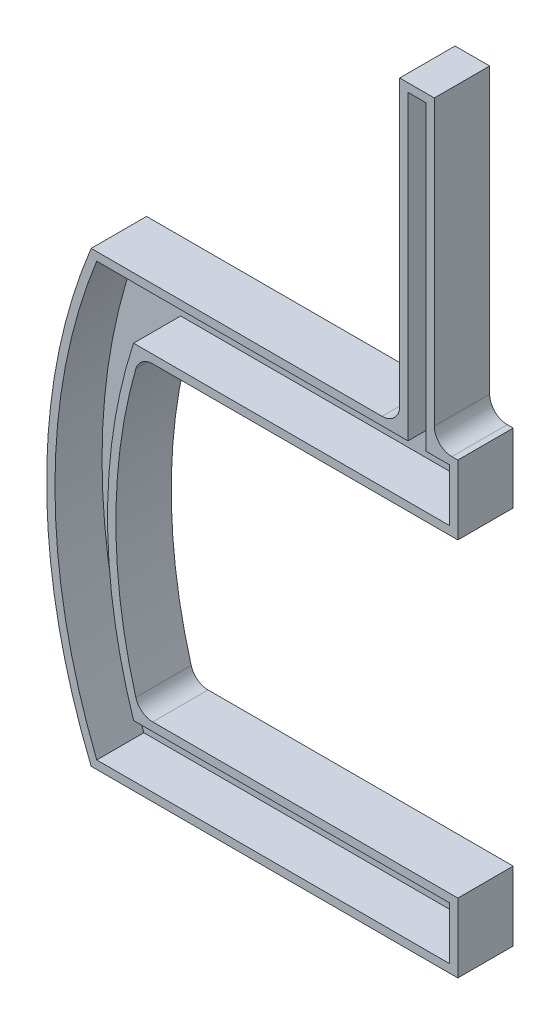
SolidWorks part; units mm, degrees
ref_plane "Front" through (0, 0, 0) normal (0, 0, 1) x (1, 0, 0)
ref_plane "Top" through (0, 0, 0) normal (0, 1, 0) x (1, 0, 0)
ref_plane "Right" through (0, 0, 0) normal (1, 0, 0) x (0, 0, -1)
sketch "Sketch1" plane through (0, 0, 0) normal (0, 0, 1) x (1, 0, 0)
  line L0 (-195.9158, 81) -> (-84.5, 81)
  line L1 (-84.5, 81) -> (-84.5, 190)
  line L2 (-84.5, 190) -> (-72, 190)
  line L3 (-72, 190) -> (-72, 81)
  line L4 (-63.5, 56) -> (-178.418, 56)
  line L5 (0, 0) -> (0, 36.5709) construction
  line L6 (0, 0) -> (56.3741, 0) construction
  line L7 (-63.5, -56) -> (-178.418, -56)
  line L8 (-195.9158, -81) -> (-63.5, -81)
  line L10 (-63.5, -56) -> (-63.5, -81)
  line L12 (-72, 81) -> (-63.5, 81)
  line L13 (-63.5, 81) -> (-63.5, 56)
  arc A0 (-195.9158, 81) -> (-195.9158, -81) centre (0, 0) ccw
  arc A1 (-178.418, 56) -> (-178.418, -56) centre (0, 0) ccw
  dimension "D1" = 424
  dimension "D2" = 374
  dimension "D3" = 81
  dimension "D4" = 25
  dimension "D5" = 12.5
  dimension "D6" = 72
  dimension "D7" = 190
  dimension "D8" = 63.5
extrude "Boss-Extrude1" add sketch "Sketch1" along normal blind 20
sketch "Sketch2" plane through (0, 0, 20) normal (0, 0, 1) x (1, 0, 0)
  line L20 (-66.5, 78) -> (-75, 78)
  line L21 (-75, 78) -> (-75, 187)
  line L22 (-75, 187) -> (-81.5, 187)
  line L23 (-81.5, 187) -> (-81.5, 78)
  line L24 (-81.5, 78) -> (-193.8995, 78)
  line L25 (-193.8995, -78) -> (-66.5, -78)
  line L26 (-66.5, -78) -> (-66.5, -59)
  line L27 (-66.5, -59) -> (-180.6073, -59)
  line L28 (-180.6073, 59) -> (-66.5, 59)
  line L29 (-66.5, 59) -> (-66.5, 78)
  line L30 (-66.5, 78) -> (-75, 78)
  line L31 (-75, 78) -> (-75, 187)
  line L32 (-75, 187) -> (-81.5, 187)
  line L33 (-81.5, 187) -> (-81.5, 78)
  line L34 (-81.5, 78) -> (-193.8995, 78)
  line L35 (-193.8995, -78) -> (-66.5, -78)
  line L36 (-66.5, -78) -> (-66.5, -59)
  line L37 (-66.5, -59) -> (-180.6073, -59)
  line L38 (-180.6073, 59) -> (-66.5, 59)
  line L39 (-66.5, 59) -> (-66.5, 78)
  arc A4 (-193.8995, 78) -> (-193.8995, -78) centre (0, 0) ccw
  arc A5 (-180.6073, 59) -> (-180.6073, -59) centre (0, 0) ccw
  arc A6 (-193.8995, 78) -> (-193.8995, -78) centre (0, 0) ccw
  arc A7 (-180.6073, 59) -> (-180.6073, -59) centre (0, 0) ccw
  dimension "D1" = 3
extrude "Cut-Extrude1" cut sketch "Sketch2" against normal offset from surface (17 mm away) 3 up to face at (-111.6945, 45.1667, 0)
fillet "Fillet1" radius 6.35 4 edges at (-72, 81, 10) (-84.5, 81, 10) (-178.418, -56, 10) (-178.418, 56, 10)
